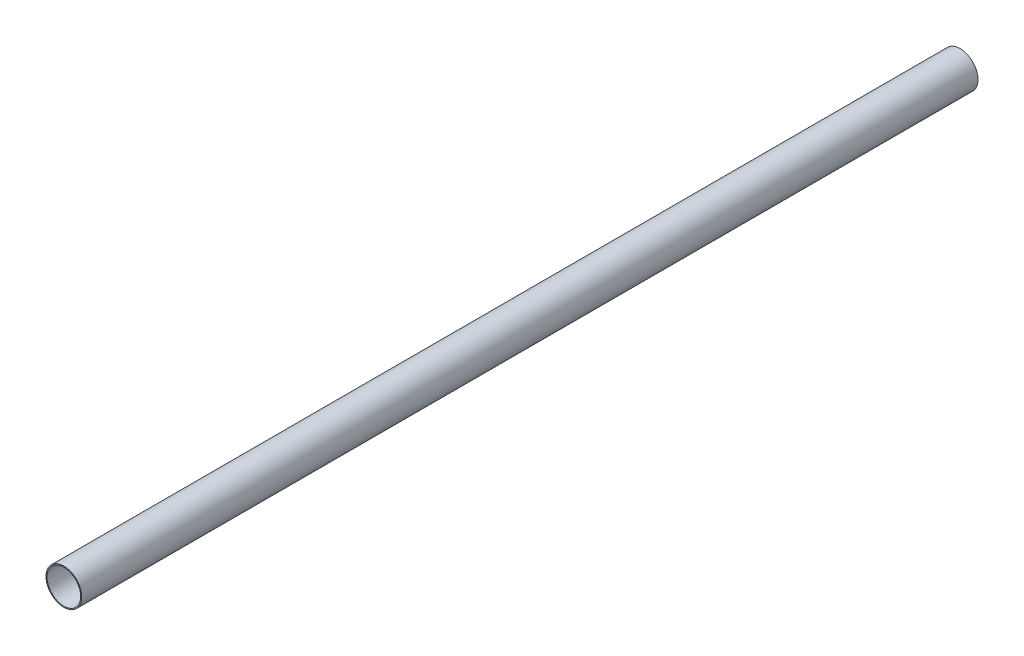
SolidWorks part; units mm, degrees
ref_plane "Front" through (0, 0, 0) normal (0, 0, 1) x (1, 0, 0)
ref_plane "Top" through (0, 0, 0) normal (0, 1, 0) x (1, 0, 0)
ref_plane "Side" through (0, 0, 0) normal (1, 0, 0) x (0, 0, -1)
sketch "PipeSketch" plane through (0, 0, 0) normal (0, 0, 1) x (1, 0, 0)
  circle A0 centre (0, 0) radius 109.474
  circle A1 centre (0, 0) radius 103.124
  dimension "OuterDiameter" = 218.948
  dimension "InnerDiameter" = 206.248
extrude "Extrusion" add sketch "PipeSketch" along normal blind 5486.4
sketch "FilterSketch" plane through (0, 0, 0) normal (0, 0, 1) x (1, 0, 0)
  circle A0 centre (0, 0) radius 101.6 construction
  dimension "NominalDiameter" = 203.2
sketch "Sketch1" [suppressed] plane through (-844.7407, -844.7407, 0) normal (-0.7071, -0.7071, 0) x (0.7071, -0.7071, 0)
  circle A0 centre (0, 1374.1) radius 103.124 construction
  circle A1 centre (0, 1374.1) radius 103.124
extrude "Cut-Extrude1" [suppressed] cut sketch "Sketch1" against normal up to surface
sketch "Sketch2" [suppressed] plane through (-971.6354, 971.6354, 0) normal (-0.7071, 0.7071, 0) x (-0.7071, -0.7071, 0)
  circle A0 centre (0, 1194.6437) radius 109.474 construction
  circle A1 centre (0, 1194.6437) radius 109.474
extrude "Cut-Extrude2" [suppressed] cut sketch "Sketch2" against normal through all
